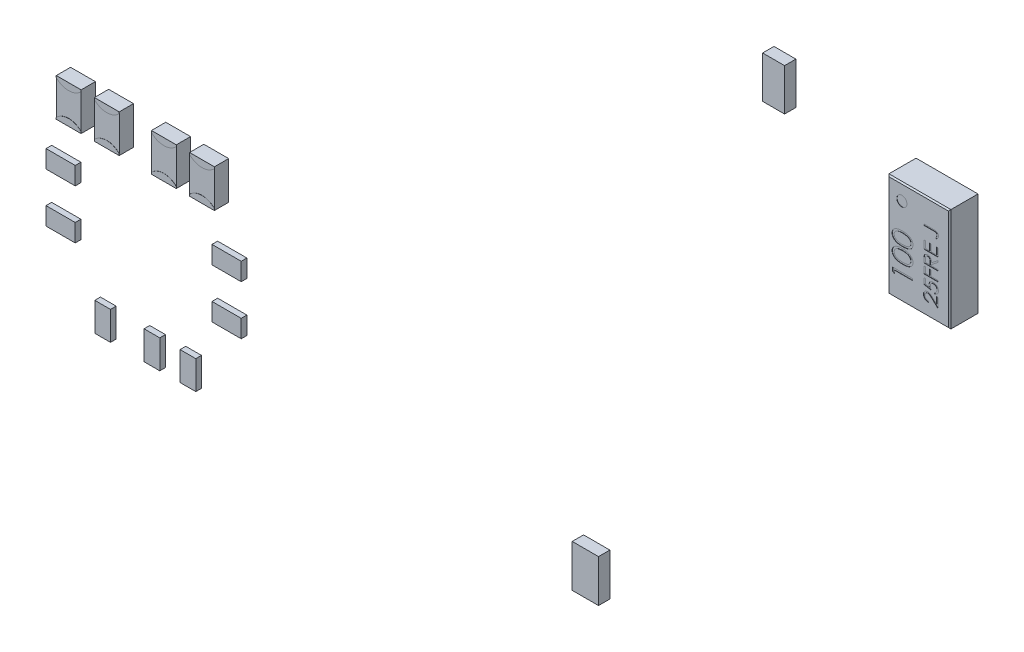
SolidWorks part; units mm, degrees
ref_plane "Płaszczyzna przednia" through (0, 0, 0) normal (0, 0, 1) x (1, 0, 0)
ref_plane "Płaszczyzna górna" through (0, 0, 0) normal (0, 1, 0) x (1, 0, 0)
ref_plane "Płaszczyzna prawa" through (0, 0, 0) normal (1, 0, 0) x (0, 0, -1)
sketch "Szkic1" plane through (0, 0, 0) normal (0, 0, 1) x (1, 0, 0)
  line L0 (-30.6267, -15.7202) -> (-30.6267, -14.4681)
  line L1 (28.3164, 18.7359) -> (28.3164, 11.4351)
  line L2 (28.3164, 11.4351) -> (32.6901, 11.4351)
  line L3 (32.6901, 11.4351) -> (32.6901, 18.7359)
  line L4 (32.6901, 18.7359) -> (28.3164, 18.7359)
  line L5 (18.2904, 20.5527) -> (18.2904, 17.592)
  line L6 (18.2904, 17.592) -> (19.8381, 17.592)
  line L7 (19.8381, 17.592) -> (19.8381, 20.5527)
  line L8 (19.8381, 20.5527) -> (18.2904, 20.5527)
  line L9 (4.8506, -16.0229) -> (4.8506, -19.0169)
  line L10 (4.8506, -19.0169) -> (6.708, -19.0169)
  line L11 (6.708, -19.0169) -> (6.708, -16.0229)
  line L12 (6.708, -16.0229) -> (4.8506, -16.0229)
  line L13 (-31.357, -5.5463) -> (-31.357, -8.22)
  line L14 (-31.357, -8.22) -> (-29.6047, -8.22)
  line L15 (-29.6047, -8.22) -> (-29.6047, -5.5463)
  line L16 (-29.6047, -5.5463) -> (-31.357, -5.5463)
  line L17 (-32.6901, -10.9811) -> (-32.6901, -12.2333)
  line L18 (-32.6901, -12.2333) -> (-30.6267, -12.2333)
  line L19 (-30.6267, -12.2333) -> (-30.6267, -10.9811)
  line L20 (-30.6267, -10.9811) -> (-32.6901, -10.9811)
  line L21 (-23.2279, -18.5357) -> (-23.2279, -20.5527)
  line L22 (-23.2279, -20.5527) -> (-22.1186, -20.5527)
  line L23 (-22.1186, -20.5527) -> (-22.1186, -18.5357)
  line L24 (-22.1186, -18.5357) -> (-23.2279, -18.5357)
  line L25 (-32.6901, -14.4681) -> (-32.6901, -15.7202)
  line L26 (-30.6267, -14.4681) -> (-32.6901, -14.4681)
  line L27 (-32.6901, -15.7202) -> (-30.6267, -15.7202)
  line L28 (-20.9748, -15.7202) -> (-18.9114, -15.7202)
  line L29 (-18.9114, -12.2333) -> (-18.9114, -10.9811)
  line L30 (-18.9114, -10.9811) -> (-20.9748, -10.9811)
  line L31 (-18.9114, -14.4681) -> (-20.9748, -14.4681)
  line L32 (-20.9748, -12.2333) -> (-18.9114, -12.2333)
  line L33 (-20.9748, -10.9811) -> (-20.9748, -12.2333)
  line L34 (-18.9114, -15.7202) -> (-18.9114, -14.4681)
  line L35 (-20.9748, -14.4681) -> (-20.9748, -15.7202)
  line L36 (-28.6679, -8.22) -> (-26.9156, -8.22)
  line L37 (-28.6679, -5.5463) -> (-28.6679, -8.22)
  line L38 (-26.9156, -5.5463) -> (-28.6679, -5.5463)
  line L39 (-26.9156, -8.22) -> (-26.9156, -5.5463)
  line L40 (-21.9501, -5.5463) -> (-21.9501, -8.22)
  line L41 (-22.8869, -5.5463) -> (-24.6392, -5.5463)
  line L42 (-24.6392, -8.22) -> (-22.8869, -8.22)
  line L43 (-20.1978, -8.22) -> (-20.1978, -5.5463)
  line L44 (-21.9501, -8.22) -> (-20.1978, -8.22)
  line L45 (-22.8869, -8.22) -> (-22.8869, -5.5463)
  line L46 (-20.1978, -5.5463) -> (-21.9501, -5.5463)
  line L47 (-24.6392, -5.5463) -> (-24.6392, -8.22)
  line L48 (-24.6598, -18.5357) -> (-25.7691, -18.5357)
  line L49 (-25.7691, -20.5527) -> (-24.6598, -20.5527)
  line L50 (-25.7691, -18.5357) -> (-25.7691, -20.5527)
  line L51 (-24.6598, -20.5527) -> (-24.6598, -18.5357)
  line L52 (-28.138, -20.5527) -> (-28.138, -18.5357)
  line L53 (-29.2473, -20.5527) -> (-28.138, -20.5527)
  line L54 (-29.2473, -18.5357) -> (-29.2473, -20.5527)
  line L55 (-28.138, -18.5357) -> (-29.2473, -18.5357)
extrude "Dodanie-wyciągnięcie1" add sketch "Szkic1" along normal blind 2 contours L3 L4 L1 L2
chamfer "Sfazowanie1" distance 0.09 angle 45 4 edges at (30.5032, 11.4351, 2) (28.3164, 15.0855, 2) (30.5032, 18.7359, 2) (32.6901, 15.0855, 2)
sketch "Szkic2" plane through (0, 0, 2) normal (0, 0, 1) x (1, 0, 0)
  line L0 (30.0649, 12.1073) -> (30.0649, 16.5277) construction
  line L1 (31.8715, 12.2789) -> (31.8715, 17.6076) construction
  circle A0 centre (29.3181, 17.6076) radius 0.358
  text T0 " 100" font "Century Gothic" height 1.4
  text T1 "25FRE J" font "Century Gothic" height 1
extrude "Wytnij-wyciągnięcie1" cut sketch "Szkic2" against normal blind 0.02
sketch "Szkic3" plane through (0, 11.4351, 0) normal (0, -1, 0) x (1, 0, 0)
  line L0 (28.3164, 0) -> (32.6901, 0) construction
  line L1 (29.2671, 1.0344) -> (31.7197, 1.0344)
  line L2 (29.2671, 1.0344) -> (29.2671, 0)
  line L3 (29.2671, 0) -> (31.7197, 0)
  line L4 (31.7197, 1.0344) -> (31.7197, 0)
  line L5 (29.2671, 1.0344) -> (31.7197, 0) construction
  line L6 (29.2671, 0) -> (31.7197, 1.0344) construction
  point P0 (30.4934, 0.5172)
extrude "Dodanie-wyciągnięcie2" add sketch "Szkic3" along normal blind 0.1 separate body
sketch "Szkic4" plane through (0, 0, 0) normal (0, 0, 1) x (1, 0, 0)
  line L4 (4.8506, -16.0229) -> (4.8506, -19.0169)
  line L5 (4.8506, -19.0169) -> (6.708, -19.0169)
  line L6 (6.708, -19.0169) -> (6.708, -16.0229)
  line L7 (6.708, -16.0229) -> (4.8506, -16.0229)
  line L8 (4.8506, -16.0229) -> (4.8506, -19.0169)
  line L9 (4.8506, -19.0169) -> (6.708, -19.0169)
  line L10 (6.708, -19.0169) -> (6.708, -16.0229)
  line L11 (6.708, -16.0229) -> (4.8506, -16.0229)
  line L12 (18.2904, 20.5527) -> (18.2904, 17.592)
  line L13 (18.2904, 17.592) -> (19.8381, 17.592)
  line L14 (19.8381, 17.592) -> (19.8381, 20.5527)
  line L15 (19.8381, 20.5527) -> (18.2904, 20.5527)
  line L16 (18.2904, 20.5527) -> (18.2904, 17.592)
  line L17 (18.2904, 17.592) -> (19.8381, 17.592)
  line L18 (19.8381, 17.592) -> (19.8381, 20.5527)
  line L19 (19.8381, 20.5527) -> (18.2904, 20.5527)
  dimension "D1" = 0
  dimension "D2" = 0
extrude "Dodanie-wyciągnięcie3" add sketch "Szkic4" along normal blind 0.8 separate body
sketch "Szkic5" plane through (0, 0, 0) normal (0, 0, 1) x (1, 0, 0)
  line L52 (-29.6047, -8.22) -> (-29.6047, -5.5463)
  line L53 (-31.357, -8.22) -> (-29.6047, -8.22)
  line L54 (-31.357, -5.5463) -> (-31.357, -8.22)
  line L55 (-29.6047, -5.5463) -> (-31.357, -5.5463)
  line L56 (-29.6047, -8.22) -> (-29.6047, -5.5463)
  line L57 (-31.357, -8.22) -> (-29.6047, -8.22)
  line L58 (-31.357, -5.5463) -> (-31.357, -8.22)
  line L59 (-29.6047, -5.5463) -> (-31.357, -5.5463)
  line L68 (-22.8869, -5.5463) -> (-24.6392, -5.5463)
  line L69 (-24.6392, -5.5463) -> (-24.6392, -8.22)
  line L70 (-24.6392, -8.22) -> (-22.8869, -8.22)
  line L71 (-22.8869, -8.22) -> (-22.8869, -5.5463)
  line L72 (-22.8869, -5.5463) -> (-24.6392, -5.5463)
  line L73 (-24.6392, -5.5463) -> (-24.6392, -8.22)
  line L74 (-24.6392, -8.22) -> (-22.8869, -8.22)
  line L75 (-22.8869, -8.22) -> (-22.8869, -5.5463)
  line L76 (-21.9501, -5.5463) -> (-21.9501, -8.22)
  line L77 (-21.9501, -8.22) -> (-20.1978, -8.22)
  line L78 (-20.1978, -8.22) -> (-20.1978, -5.5463)
  line L79 (-20.1978, -5.5463) -> (-21.9501, -5.5463)
  line L80 (-21.9501, -5.5463) -> (-21.9501, -8.22)
  line L81 (-21.9501, -8.22) -> (-20.1978, -8.22)
  line L82 (-20.1978, -8.22) -> (-20.1978, -5.5463)
  line L83 (-20.1978, -5.5463) -> (-21.9501, -5.5463)
  line L84 (-28.6679, -8.22) -> (-26.9156, -8.22)
  line L85 (-26.9156, -8.22) -> (-26.9156, -5.5463)
  line L86 (-26.9156, -5.5463) -> (-28.6679, -5.5463)
  line L87 (-28.6679, -5.5463) -> (-28.6679, -8.22)
  line L88 (-28.6679, -8.22) -> (-26.9156, -8.22)
  line L89 (-26.9156, -8.22) -> (-26.9156, -5.5463)
  line L90 (-26.9156, -5.5463) -> (-28.6679, -5.5463)
  line L91 (-28.6679, -5.5463) -> (-28.6679, -8.22)
  dimension "D7" = 0
  dimension "D9" = 0
  dimension "D10" = 0
  dimension "D11" = 0
extrude "Dodanie-wyciągnięcie4" add sketch "Szkic5" along normal blind 1 separate body
sketch "Szkic6" plane through (0, 0, 1) normal (0, 0, 1) x (1, 0, 0)
  line L0 (-31.357, -6.8831) -> (-29.6047, -6.8831) construction
  line L1 (-31.357, -5.5463) -> (-31.357, -8.22) construction
  line L2 (-29.6047, -8.22) -> (-29.6047, -5.5463) construction
  line L3 (-31.357, -8.22) -> (-29.6047, -8.22) construction
  line L4 (-29.6047, -5.5463) -> (-31.357, -5.5463) construction
  line L5 (-31.357, -8.22) -> (-29.6047, -8.22)
  line L6 (-31.357, -5.5463) -> (-31.357, -5.6629)
  line L7 (-29.6047, -8.22) -> (-29.6047, -8.1033)
  line L8 (-29.6047, -5.5463) -> (-31.357, -5.5463)
  line L9 (-28.6679, -5.5463) -> (-28.6679, -5.6629)
  line L10 (-26.9156, -8.22) -> (-26.9156, -8.1033)
  line L11 (-26.9156, -5.5463) -> (-28.6679, -5.5463)
  line L12 (-28.6679, -8.22) -> (-26.9156, -8.22)
  line L13 (-28.6679, -6.8831) -> (-26.9156, -6.8831) construction
  line L14 (-31.357, -8.1033) -> (-31.357, -8.22)
  line L15 (-29.6047, -5.6629) -> (-29.6047, -5.5463)
  line L16 (-28.6679, -8.1033) -> (-28.6679, -8.22)
  line L17 (-26.9156, -5.6629) -> (-26.9156, -5.5463)
  line L18 (-22.8869, -5.5463) -> (-24.6392, -5.5463)
  line L19 (-20.1978, -5.6629) -> (-20.1978, -5.5463)
  line L20 (-21.9501, -5.5463) -> (-21.9501, -5.6629)
  line L21 (-21.9501, -8.1033) -> (-21.9501, -8.22)
  line L22 (-21.9501, -6.8831) -> (-20.1978, -6.8831) construction
  line L23 (-21.9501, -8.22) -> (-20.1978, -8.22)
  line L24 (-22.8869, -5.6629) -> (-22.8869, -5.5463)
  line L25 (-24.6392, -5.5463) -> (-24.6392, -5.6629)
  line L26 (-24.6392, -8.1033) -> (-24.6392, -8.22)
  line L27 (-20.1978, -8.22) -> (-20.1978, -8.1033)
  line L28 (-20.1978, -5.5463) -> (-21.9501, -5.5463)
  line L29 (-24.6392, -6.8831) -> (-22.8869, -6.8831) construction
  line L30 (-22.8869, -8.22) -> (-22.8869, -8.1033)
  line L31 (-24.6392, -8.22) -> (-22.8869, -8.22)
  arc A0 (-29.6047, -8.1033) -> (-31.357, -8.1033) centre (-30.4809, -8.959) ccw
  arc A1 (-29.6047, -5.6629) -> (-31.357, -5.6629) centre (-30.4809, -4.8073) cw
  arc A2 (-26.9156, -5.6629) -> (-28.6679, -5.6629) centre (-27.7918, -4.8073) cw
  arc A3 (-26.9156, -8.1033) -> (-28.6679, -8.1033) centre (-27.7918, -8.959) ccw
  arc A4 (-20.1978, -5.6629) -> (-21.9501, -5.6629) centre (-21.074, -4.8073) cw
  arc A5 (-22.8869, -5.6629) -> (-24.6392, -5.6629) centre (-23.7631, -4.8073) cw
  arc A6 (-22.8869, -8.1033) -> (-24.6392, -8.1033) centre (-23.7631, -8.959) ccw
  arc A7 (-20.1978, -8.1033) -> (-21.9501, -8.1033) centre (-21.074, -8.959) ccw
extrude "Dodanie-wyciągnięcie5" add sketch "Szkic6" along normal blind 0.01 separate body
sketch "Szkic7" plane through (0, 0, 0) normal (0, 0, 1) x (1, 0, 0)
  line L28 (-18.9114, -12.2333) -> (-18.9114, -10.9811)
  line L29 (-18.9114, -10.9811) -> (-20.9748, -10.9811)
  line L30 (-20.9748, -10.9811) -> (-20.9748, -12.2333)
  line L31 (-20.9748, -12.2333) -> (-18.9114, -12.2333)
  line L32 (-18.9114, -12.2333) -> (-18.9114, -10.9811)
  line L33 (-18.9114, -10.9811) -> (-20.9748, -10.9811)
  line L34 (-20.9748, -10.9811) -> (-20.9748, -12.2333)
  line L35 (-20.9748, -12.2333) -> (-18.9114, -12.2333)
  line L36 (-23.2279, -18.5357) -> (-23.2279, -20.5527)
  line L37 (-23.2279, -20.5527) -> (-22.1186, -20.5527)
  line L38 (-22.1186, -20.5527) -> (-22.1186, -18.5357)
  line L39 (-22.1186, -18.5357) -> (-23.2279, -18.5357)
  line L40 (-23.2279, -18.5357) -> (-23.2279, -20.5527)
  line L41 (-23.2279, -20.5527) -> (-22.1186, -20.5527)
  line L42 (-22.1186, -20.5527) -> (-22.1186, -18.5357)
  line L43 (-22.1186, -18.5357) -> (-23.2279, -18.5357)
  line L44 (-32.6901, -12.2333) -> (-30.6267, -12.2333)
  line L45 (-30.6267, -12.2333) -> (-30.6267, -10.9811)
  line L46 (-30.6267, -10.9811) -> (-32.6901, -10.9811)
  line L47 (-32.6901, -10.9811) -> (-32.6901, -12.2333)
  line L48 (-32.6901, -12.2333) -> (-30.6267, -12.2333)
  line L49 (-30.6267, -12.2333) -> (-30.6267, -10.9811)
  line L50 (-30.6267, -10.9811) -> (-32.6901, -10.9811)
  line L51 (-32.6901, -10.9811) -> (-32.6901, -12.2333)
  line L60 (-30.6267, -15.7202) -> (-30.6267, -14.4681)
  line L61 (-30.6267, -14.4681) -> (-32.6901, -14.4681)
  line L62 (-32.6901, -14.4681) -> (-32.6901, -15.7202)
  line L63 (-32.6901, -15.7202) -> (-30.6267, -15.7202)
  line L64 (-30.6267, -15.7202) -> (-30.6267, -14.4681)
  line L65 (-30.6267, -14.4681) -> (-32.6901, -14.4681)
  line L66 (-32.6901, -14.4681) -> (-32.6901, -15.7202)
  line L67 (-32.6901, -15.7202) -> (-30.6267, -15.7202)
  line L92 (-20.9748, -15.7202) -> (-18.9114, -15.7202)
  line L93 (-18.9114, -15.7202) -> (-18.9114, -14.4681)
  line L94 (-18.9114, -14.4681) -> (-20.9748, -14.4681)
  line L95 (-20.9748, -14.4681) -> (-20.9748, -15.7202)
  line L96 (-20.9748, -15.7202) -> (-18.9114, -15.7202)
  line L97 (-18.9114, -15.7202) -> (-18.9114, -14.4681)
  line L98 (-18.9114, -14.4681) -> (-20.9748, -14.4681)
  line L99 (-20.9748, -14.4681) -> (-20.9748, -15.7202)
  line L100 (-28.138, -20.5527) -> (-28.138, -18.5357)
  line L101 (-28.138, -18.5357) -> (-29.2473, -18.5357)
  line L102 (-29.2473, -18.5357) -> (-29.2473, -20.5527)
  line L103 (-29.2473, -20.5527) -> (-28.138, -20.5527)
  line L104 (-28.138, -20.5527) -> (-28.138, -18.5357)
  line L105 (-28.138, -18.5357) -> (-29.2473, -18.5357)
  line L106 (-29.2473, -18.5357) -> (-29.2473, -20.5527)
  line L107 (-29.2473, -20.5527) -> (-28.138, -20.5527)
  line L108 (-24.6598, -18.5357) -> (-25.7691, -18.5357)
  line L109 (-25.7691, -18.5357) -> (-25.7691, -20.5527)
  line L110 (-25.7691, -20.5527) -> (-24.6598, -20.5527)
  line L111 (-24.6598, -20.5527) -> (-24.6598, -18.5357)
  line L112 (-24.6598, -18.5357) -> (-25.7691, -18.5357)
  line L113 (-25.7691, -18.5357) -> (-25.7691, -20.5527)
  line L114 (-25.7691, -20.5527) -> (-24.6598, -20.5527)
  line L115 (-24.6598, -20.5527) -> (-24.6598, -18.5357)
  dimension "D4" = 0
  dimension "D5" = 0
  dimension "D6" = 0
  dimension "D8" = 0
  dimension "D12" = 0
  dimension "D13" = 0
  dimension "D14" = 0
extrude "Dodanie-wyciągnięcie6" add sketch "Szkic7" along normal blind 0.4 separate body
